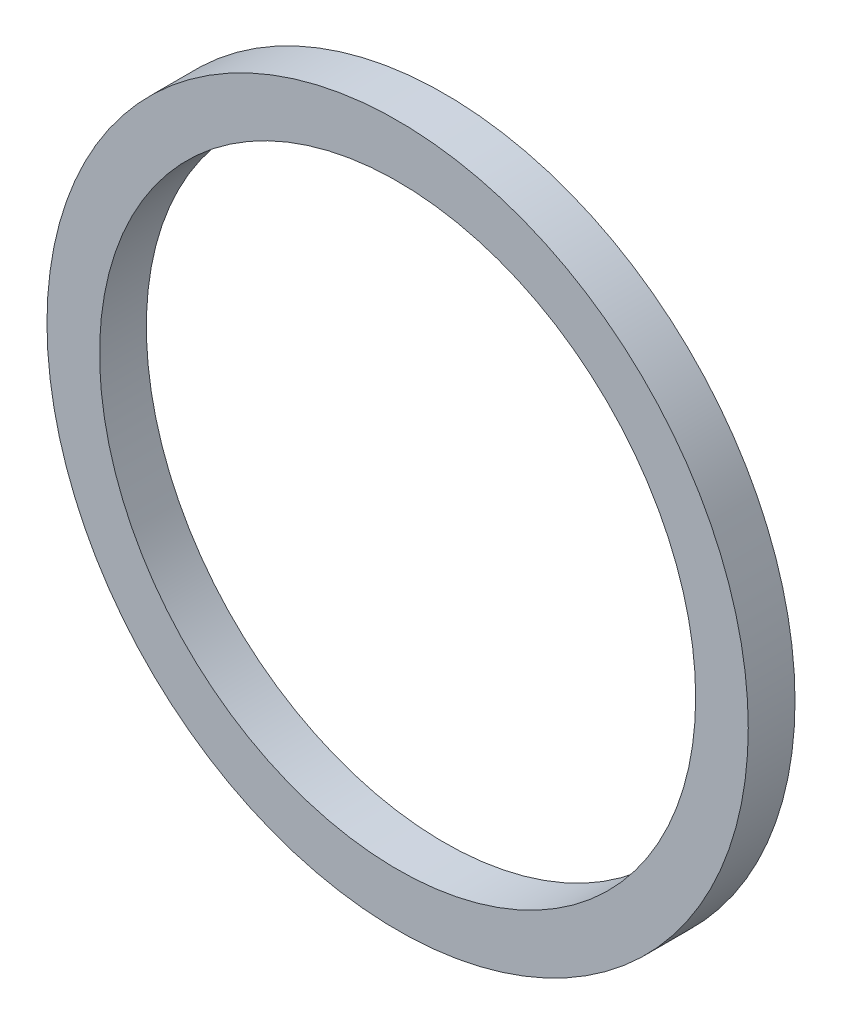
SolidWorks part; units mm, degrees
ref_plane "Ebene vorne" through (0, 0, 0) normal (0, 0, 1) x (1, 0, 0)
ref_plane "Ebene oben" through (0, 0, 0) normal (0, 1, 0) x (1, 0, 0)
ref_plane "Ebene rechts" through (0, 0, 0) normal (1, 0, 0) x (0, 0, -1)
sketch "Skizze1" plane through (0, 0, 0) normal (0, 0, 1) x (1, 0, 0)
  circle A0 centre (0, 0) radius 12.75
  circle A2 centre (0, 0) radius 15
  dimension "D1" = 25.5
  dimension "D2" = 30
extrude "Aufsatz-Linear austragen1" add sketch "Skizze1" along normal blind 2 contours A2 A0
